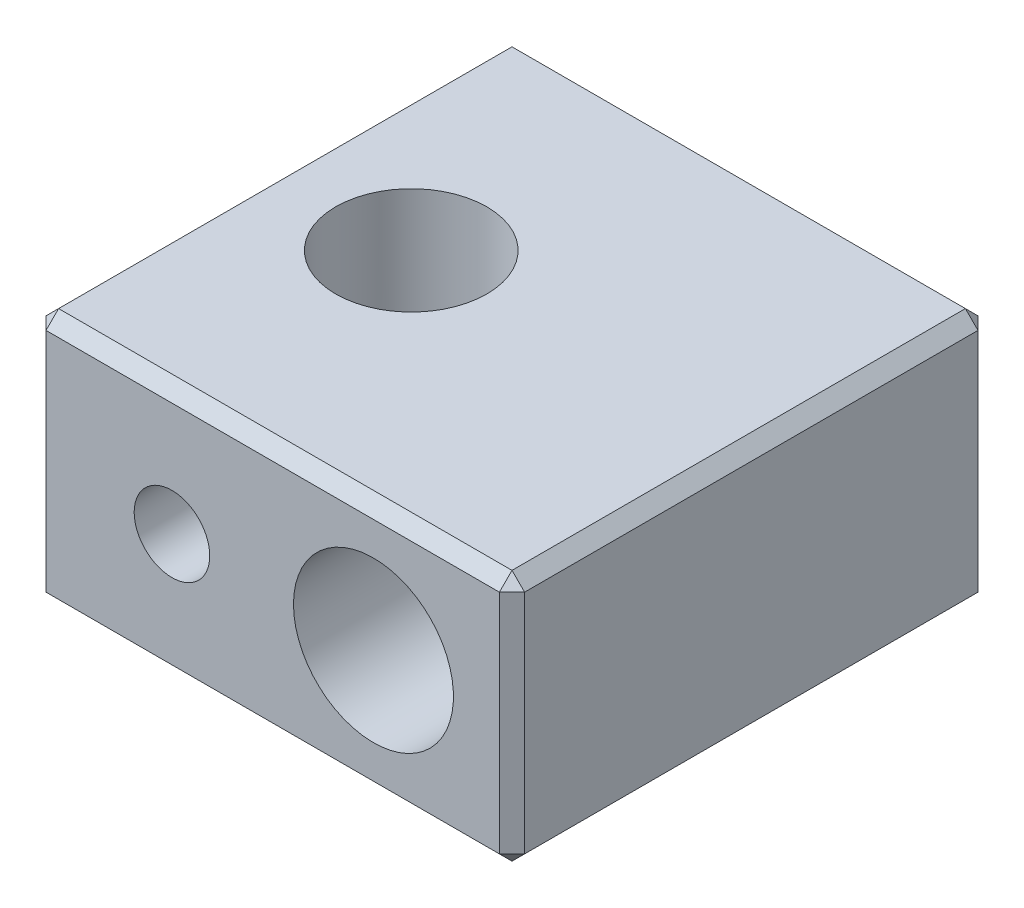
SolidWorks part; units mm, degrees
material "6061 Alloy"
ref_plane "Front Plane" through (0, 0, 0) normal (0, 0, 1) x (1, 0, 0)
ref_plane "Top Plane" through (0, 0, 0) normal (0, 1, 0) x (1, 0, 0)
ref_plane "Right Plane" through (0, 0, 0) normal (1, 0, 0) x (0, 0, -1)
sketch "Sketch2" plane through (0, 0, 0) normal (0, 1, 0) x (1, 0, 0)
  line L0 (-1000, 0) -> (49000, 0) construction
  line L3 (-9.5, 9.5) -> (9.5, 9.5)
  line L4 (-9.5, 9.5) -> (-9.5, -9.5)
  line L5 (-9.5, -9.5) -> (9.5, -9.5)
  line L6 (9.5, 9.5) -> (9.5, -9.5)
  line L7 (-9.5, 9.5) -> (9.5, -9.5) construction
  line L8 (-9.5, -9.5) -> (9.5, 9.5) construction
  circle A0 centre (-4, 0) radius 3
  dimension "D3" = 4
  dimension "D4" = 6
  dimension "D1" = 19
  dimension "D2" = 19
extrude "Boss-Extrude1" add sketch "Sketch2" along normal blind 10
sketch "Sketch3" plane through (0, 0, 0) normal (0, -1, 0) x (1, 0, 0)
  circle A0 centre (-4, 0) radius 3.25
  circle A1 centre (-4, 0) radius 3 construction
  dimension "D1" = 6.5
extrude "Cut-Extrude1" cut sketch "Sketch3" against normal blind 1.5
sketch "Sketch7" plane through (0, 0, -9.5) normal (0, 0, -1) x (-1, 0, 0)
  line L2 (-9.5, 5) -> (9.5, 5) construction
  line L3 (-9.5, 10) -> (-9.5, 0) construction
  line L4 (9.5, 10) -> (9.5, 0) construction
  circle A0 centre (-4, 5) radius 3.175
  dimension "D1" = 6.35
  dimension "D3" = 4
extrude "Cut-Extrude5" cut sketch "Sketch7" against normal through all
sketch "Sketch12" plane through (0, 0, 0) normal (0, 1, 0) x (1, 0, 0)
  line L2 (-9.5, 0) -> (9.5, 0) construction
  line L3 (-9.5, 9.5) -> (-9.5, -9.5) construction
  line L4 (9.5, -9.5) -> (9.5, 9.5) construction
  circle A0 centre (4, 0) radius 1.5
  dimension "D1" = 3
  dimension "D2" = 4
extrude "Cut-Extrude9" cut sketch "Sketch12" along normal up to next
sketch "Sketch14" plane through (0, 0, 9.5) normal (0, 0, -1) x (-1, 0, 0)
  line L0 (-9.5, 5) -> (9.5, 5) construction
  line L1 (-9.5, 10) -> (-9.5, 0) construction
  line L2 (9.5, 10) -> (9.5, 0) construction
  circle A0 centre (4, 5) radius 1.5
  dimension "D1" = 4
  dimension "D3" = 3
extrude "Cut-Extrude11" cut sketch "Sketch14" along normal blind 5
chamfer "Chamfer1" distance 0.5 angle 45 12 edges at (0, 0, 9.5) (9.5, 0, 0) (0, 0, -9.5) (-9.5, 0, 0) (-9.5, 5, -9.5) (9.5, 5, -9.5) (9.5, 5, 9.5) (-9.5, 5, 9.5) (0, 10, -9.5) (9.5, 10, 0) (0, 10, 9.5) (-9.5, 10, 0)
